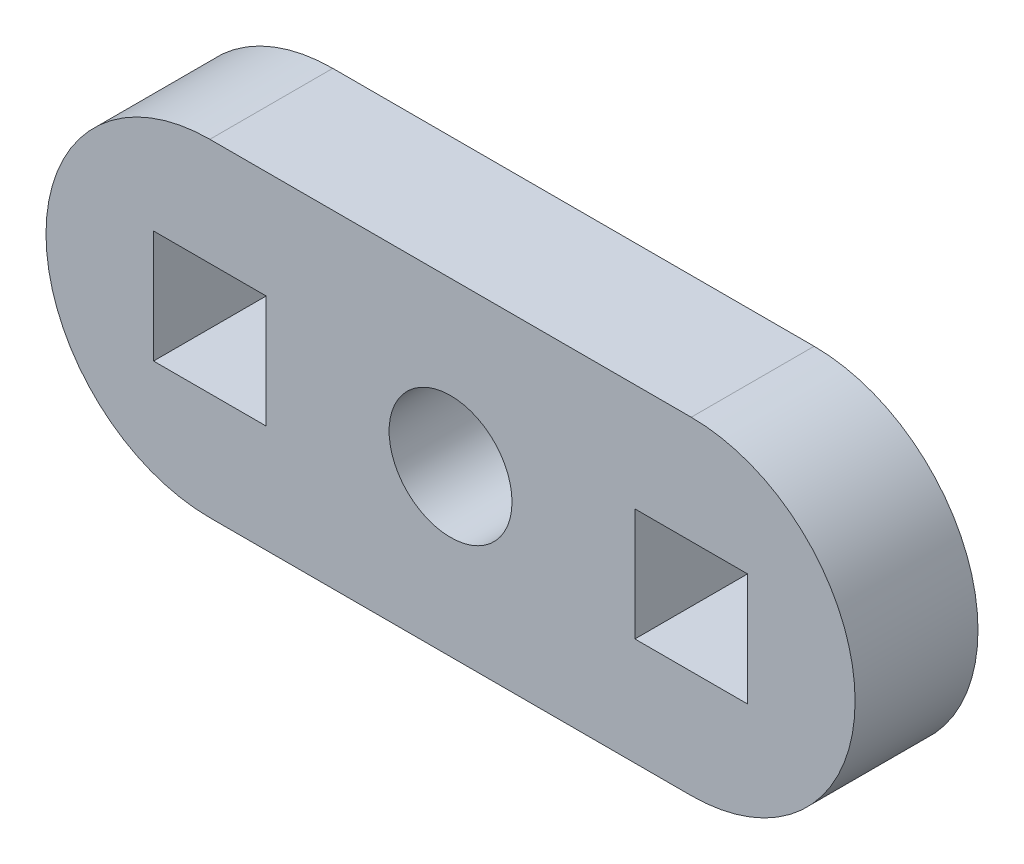
SolidWorks part; units mm, degrees
ref_plane "Front Plane" through (0, 0, 0) normal (0, 0, 1) x (1, 0, 0)
ref_plane "Top Plane" through (0, 0, 0) normal (0, 1, 0) x (1, 0, 0)
ref_plane "Right Plane" through (0, 0, 0) normal (1, 0, 0) x (0, 0, -1)
sketch "Model" plane through (0, 0, 0) normal (0, 0, 1) x (1, 0, 0)
  line L0 (27.695, 13.9509) -> (27.695, 16.7009)
  line L1 (27.695, 16.7009) -> (22.195, 16.7009)
  line L2 (22.195, 16.7009) -> (22.195, 11.2009)
  line L3 (22.195, 11.2009) -> (27.695, 11.2009)
  line L4 (27.695, 11.2009) -> (27.695, 13.9509)
  line L5 (24.945, 21.9509) -> (48.445, 21.9509)
  line L6 (24.945, 5.9509) -> (48.445, 5.9509)
  line L7 (45.695, 13.9509) -> (45.695, 16.7009)
  line L8 (45.695, 16.7009) -> (51.195, 16.7009)
  line L9 (51.195, 16.7009) -> (51.195, 11.2009)
  line L10 (51.195, 11.2009) -> (45.695, 11.2009)
  line L11 (45.695, 11.2009) -> (45.695, 13.9509)
  circle A0 centre (36.695, 13.9937) radius 3
  arc A1 (24.945, 21.9509) -> (24.945, 5.9509) centre (24.945, 13.9509) ccw
  arc A2 (48.445, 5.9509) -> (48.445, 21.9509) centre (48.445, 13.9509) ccw
extrude "Boss-Extrude1" add sketch "Model" along normal blind 6 contours L11 L10 L9 L8 L7 | A1 L6 A2 L5 | A0 | L4 L0 L1 L2 L3
